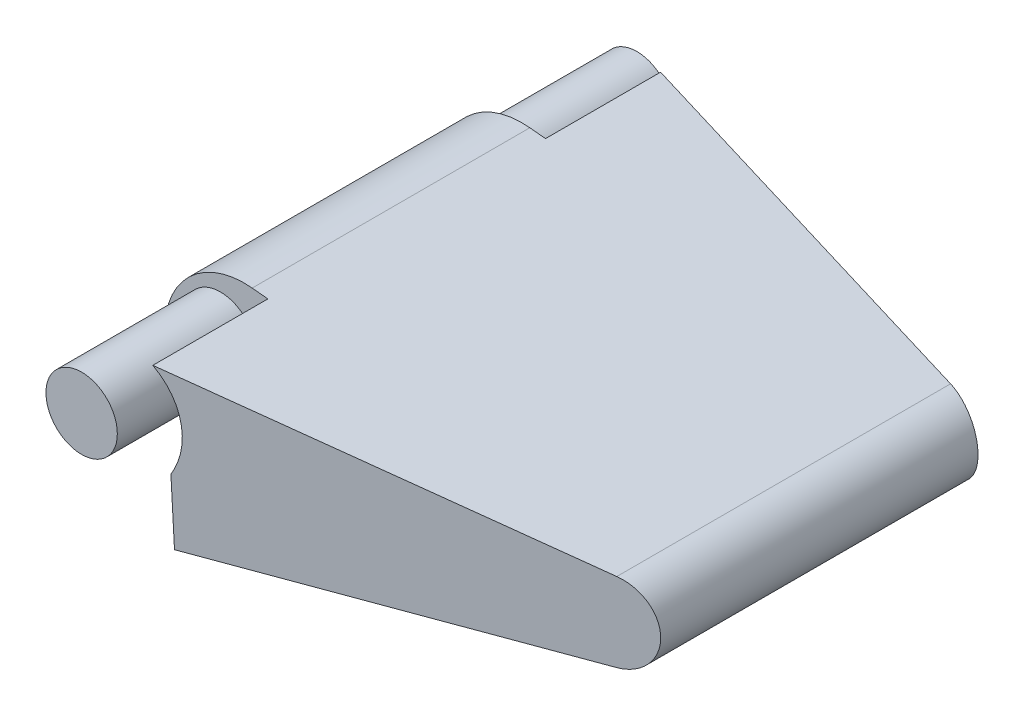
SolidWorks part; units mm, degrees
material "Brass"
ref_plane "Front Plane" through (0, 0, 0) normal (0, 0, 1) x (1, 0, 0)
ref_plane "Top Plane" through (0, 0, 0) normal (0, 1, 0) x (1, 0, 0)
ref_plane "Right Plane" through (0, 0, 0) normal (1, 0, 0) x (0, 0, -1)
sketch "Sketch2" plane through (0, 0, 0) normal (0, 0, 1) x (1, 0, 0)
  line L0 (0.635, 6.3182) -> (32.0675, 3.1591)
  line L1 (0.635, -6.3182) -> (32.0675, -3.1591)
  line L2 (0.635, 6.3182) -> (0.635, -6.3182) construction
  arc A1 (0.635, 6.3182) -> (0.635, -6.3182) centre (0, 0) ccw
  arc A2 (32.0675, -3.1591) -> (32.0675, 3.1591) centre (31.75, 0) ccw
  circle A3 centre (-1.9083, 1.9207) radius 2.54
  dimension "D1" = 6.35
  dimension "D2" = 3.175
  dimension "D4" = 5.08
  dimension "D3" = 31.75
  dimension "D5" = 5.08
extrude "Boss-Extrude1" add sketch "Sketch2" along normal mid plane 44.45
sketch "Sketch3" plane through (0, 0, 0) normal (0, 1, 0) x (1, 0, 0)
  line L0 (-6.35, 22.225) -> (34.925, 12.7)
  line L1 (34.925, -22.225) -> (34.925, 22.225) construction
  line L2 (34.925, 12.7) -> (34.925, 31.6809)
  line L3 (34.925, 31.6809) -> (-6.35, 22.225)
  line L4 (-6.35, -22.225) -> (34.925, -12.7)
  line L5 (-6.35, -22.225) -> (0.635, -22.225) construction
  line L6 (34.925, -12.7) -> (34.925, -37.6369)
  line L7 (34.925, -37.6369) -> (-6.35, -22.225)
  line L8 (34.925, 12.7) -> (34.925, -12.7) construction
  line L9 (32.0675, -22.225) -> (32.0675, 22.225) construction
  point P10 (34.925, 0)
  point P14 (32.0675, 0)
  dimension "D1" = 25.4
extrude "Cut-Extrude1" cut sketch "Sketch3" against normal through all both and the other way through all
ref_plane "Plane1" through (0, 0, 25.4) normal (0, 0, 1) x (1, 0, 0)
sketch "Sketch7" plane through (0, 0, 0) normal (0, 0, 1) x (1, 0, 0)
  circle A2 centre (0, -1.5875) radius 0.9525
  dimension "D1" = 1.905
  dimension "D2" = 0
  dimension "D3" = 1.5875
extrude "Cut-Extrude5" cut sketch "Sketch7" against normal mid plane 1.905
sketch "Sketch5" plane through (0, 0, 25.4) normal (0, 0, 1) x (1, 0, 0)
  line L4 (3.0645, -0.8959) -> (3.2999, -6.0503)
  line L5 (32.0675, -3.1591) -> (0.635, -6.3182) construction
  line L6 (3.2999, -6.0503) -> (5.2108, -13.2101)
  line L7 (5.2108, -13.2101) -> (-7.6233, -5.7183)
  line L8 (-7.6233, -5.7183) -> (-7.6233, 1.9207)
  arc A3 (3.0645, -0.8959) -> (-7.6233, 1.9207) centre (-1.9083, 1.9207) ccw
  dimension "D1" = 11.43
ref_plane "Plane2" through (0, 0, 0.7937) normal (0, 0, 1) x (1, 0, 0)
extrude "Cut-Extrude6" cut sketch "Sketch5" against normal blind 14.2875
mirror "Mirror2" about plane through (0, 0, 0) normal (0, 0, 1) of "Cut-Extrude6"
sketch "Sketch11" plane through (0, 0, 0) normal (0, 0, 1) x (1, 0, 0)
  circle A0 centre (-1.9083, 1.9207) radius 2.8575
  circle A1 centre (-1.9083, 1.9207) radius 2.54 construction
  dimension "D1" = 5.715
extrude "Boss-Extrude2" add sketch "Sketch11" along normal mid plane 44.45
sketch "Sketch9" plane through (0, 0, 0.7937) normal (0, 0, 1) x (1, 0, 0)
  line L0 (-4.9394, 3.9906) -> (3.0645, -0.8959)
  line L1 (3.0645, -0.8959) -> (3.2999, -6.0503)
  line L2 (3.2999, -6.0503) -> (-14.4966, -7.839)
  line L3 (-14.4966, -7.839) -> (-4.9394, 3.9906)
  arc A0 (0.635, 6.3182) -> (0.635, -6.3182) centre (0, 0) ccw construction
extrude "Cut-Extrude7" cut sketch "Sketch9" along normal blind 6.35
mirror "Mirror1" about plane through (0, 0, 0) normal (0, 0, 1) of "Cut-Extrude7"
